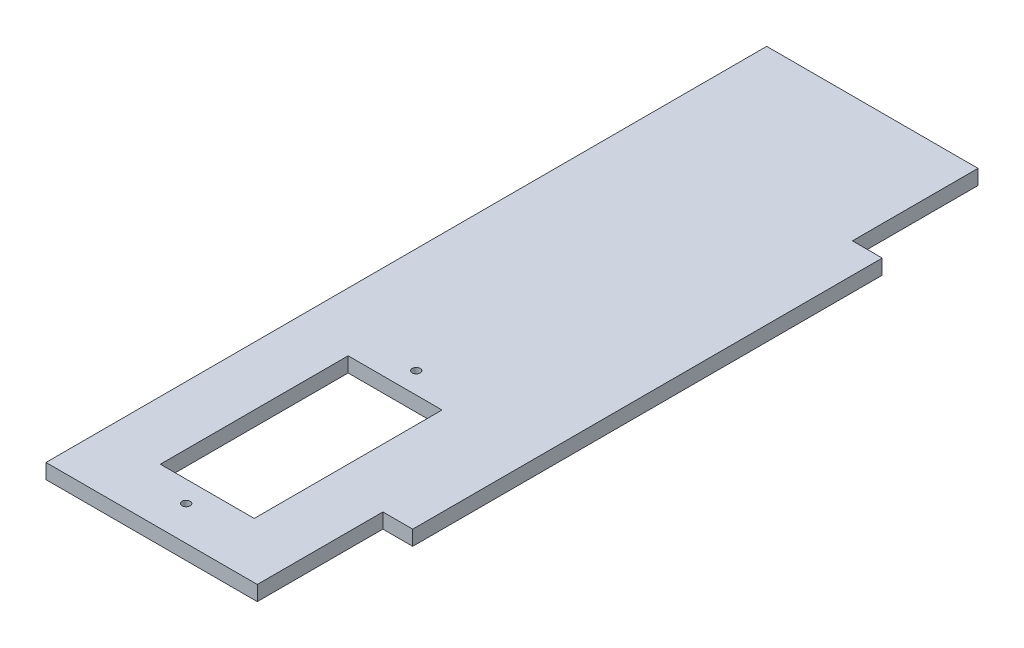
SolidWorks part; units mm, degrees
material "Cedar"
ref_plane "Front Plane" through (0, 0, 0) normal (0, 0, 1) x (1, 0, 0)
ref_plane "Top Plane" through (0, 0, 0) normal (0, 1, 0) x (1, 0, 0)
ref_plane "Right Plane" through (0, 0, 0) normal (1, 0, 0) x (0, 0, -1)
sketch "Sketch1" plane through (0, 0, 0) normal (0, 1, 0) x (1, 0, 0)
  line L0 (-22.5, 26.75) -> (22.5, 26.75)
  line L1 (22.5, 26.75) -> (22.5, 0)
  line L2 (22.5, 0) -> (28.85, 0)
  line L3 (28.85, 0) -> (28.85, -100)
  line L4 (28.85, -100) -> (22.5, -100)
  line L5 (22.5, -100) -> (22.5, -126.75)
  line L6 (22.5, -126.75) -> (-22.5, -126.75)
  line L7 (-22.5, -126.75) -> (-22.5, -100)
  line L8 (-22.5, -100) -> (-28.85, -100)
  line L9 (-28.85, -100) -> (-28.85, 0)
  line L10 (-28.85, 0) -> (-22.5, 0)
  line L11 (-22.5, 0) -> (-22.5, 26.75)
  line L12 (-22.5, 0) -> (-22.5, -100) construction
  point P11 (0, 26.75)
  point P14 (-28.85, -50)
  dimension "D1" = 6.35
  dimension "D2" = 100
  dimension "D3" = 45
  dimension "D4" = 153.5
extrude "Boss-Extrude1" add sketch "Sketch1" along normal blind 3.175 contours L11 L12 L7 L6 L5 L4 L3 L2 L1 L0
sketch "Sketch3" plane through (0, 3.175, 0) normal (0, 1, 0) x (1, 0, 0)
  line L0 (-22.5, 26.75) -> (22.5, 26.75) construction
  line L1 (10, -114.9) -> (-10, -114.9)
  line L2 (10, -114.9) -> (10, -74.9)
  line L3 (10, -74.9) -> (-10, -74.9)
  line L4 (-10, -114.9) -> (-10, -74.9)
  line L5 (10, -114.9) -> (-10, -74.9) construction
  line L6 (10, -74.9) -> (-10, -114.9) construction
  line L7 (0, -70.4) -> (0, -119.4) construction
  point P0 (0, -94.9)
  point P5 (0, -81.25)
  dimension "D1" = 108
  dimension "D2" = 6.35
  dimension "D3" = 20
  dimension "D4" = 40
  dimension "D5" = 49
extrude "Cut-Extrude1" cut sketch "Sketch3" against normal through all
hole_wizard "M1.6 Clearance Hole1" positions "Sketch5" profile "Sketch4" hole size "M1.6" standard "ANSI Metric" end condition through all
sketch "Sketch5" plane through (0, 3.175, 0) normal (0, 1, 0) x (1, 0, 0)
  point P0 (0, -70.4)
  point P3 (0, -119.4)
sketch "Sketch4" plane through (0, 3.175, 70.4) normal (1, 0, 0) x (0, 0, 1)
  line L0 (0, 0) -> (0, 3.175)
  line L1 (0, 3.175) -> (0.85, 3.175)
  line L2 (0.85, 3.175) -> (0.85, 0)
  line L5 (0.85, 0) -> (0, 0)
  line L11 (0, -6.35) -> (0, 107.95) construction
  dimension "Thru Hole Dia." = 1.7
  dimension "Thru Hole Depth" = 3.175
equation "\"length\"= 153.5mm"
equation "\"w_mach\"= 45mm"
equation "\"w_tab\"= 100mm"
equation "\"t_wood\"= 0.125in"
equation "\"t_side\"= 0.25in"
equation "\"D1@Sketch1\"=\"t_side\""
equation "\"D2@Sketch1\"=\"w_tab\""
equation "\"D3@Sketch1\"=\"w_mach\""
equation "\"D4@Sketch1\"=\"length\""
equation "\"D1@Boss-Extrude1\"=\"t_wood\""
equation "\"w_servo\"= 20mm"
equation "\"l_servo\"= 40mm"
equation "\"servocenter\"= 6.35mm"
equation "\"servoholes\"= 49mm"
equation "\"dY\"= 124mm"
equation "\"in_rad\"= 16mm"
equation "\"D1@Sketch3\"=\"dY\"-\"in_rad\""
equation "\"D2@Sketch3\"=\"servocenter\""
equation "\"D3@Sketch3\"=\"w_servo\""
equation "\"D4@Sketch3\"=\"l_servo\""
equation "\"D5@Sketch3\"=\"servoholes\""
